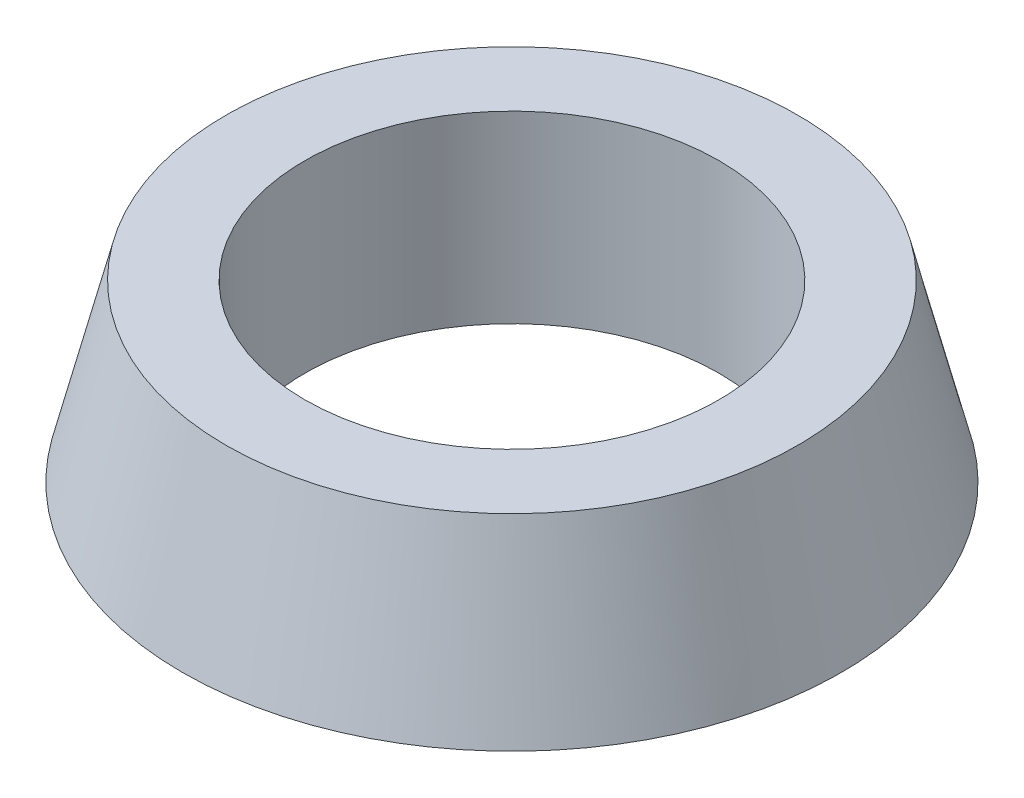
SolidWorks part; units mm, degrees
ref_plane "Front Plane" through (0, 0, 0) normal (0, 0, 1) x (1, 0, 0)
ref_plane "Top Plane" through (0, 0, 0) normal (0, 1, 0) x (1, 0, 0)
ref_plane "Right Plane" through (0, 0, 0) normal (1, 0, 0) x (0, 0, -1)
sketch "Sketch1" plane through (0, 0, 0) normal (0, 0, 1) x (1, 0, 0)
  line L0 (0, 0) -> (0, -21.6687) construction
  line L1 (22.5, 0.0653) -> (22.5, 20.0653)
  line L2 (22.5, 20.0653) -> (31.0628, 20.0653)
  line L3 (31.0628, 20.0653) -> (35.8, 1.0653)
  line L4 (35.8, 1.0653) -> (30.3, 1.0653)
  line L5 (30.3, 1.0653) -> (30.3, 0.0653)
  line L6 (30.3, 0.0653) -> (22.5, 0.0653)
  dimension "D1" = 22.5
  dimension "D2" = 20
  dimension "D3" = 7.8
  dimension "D4" = 13.3
  dimension "D5" = 104
  dimension "D6" = 19
revolve "Revolve1" add sketch "Sketch1" angle 360 about L0
